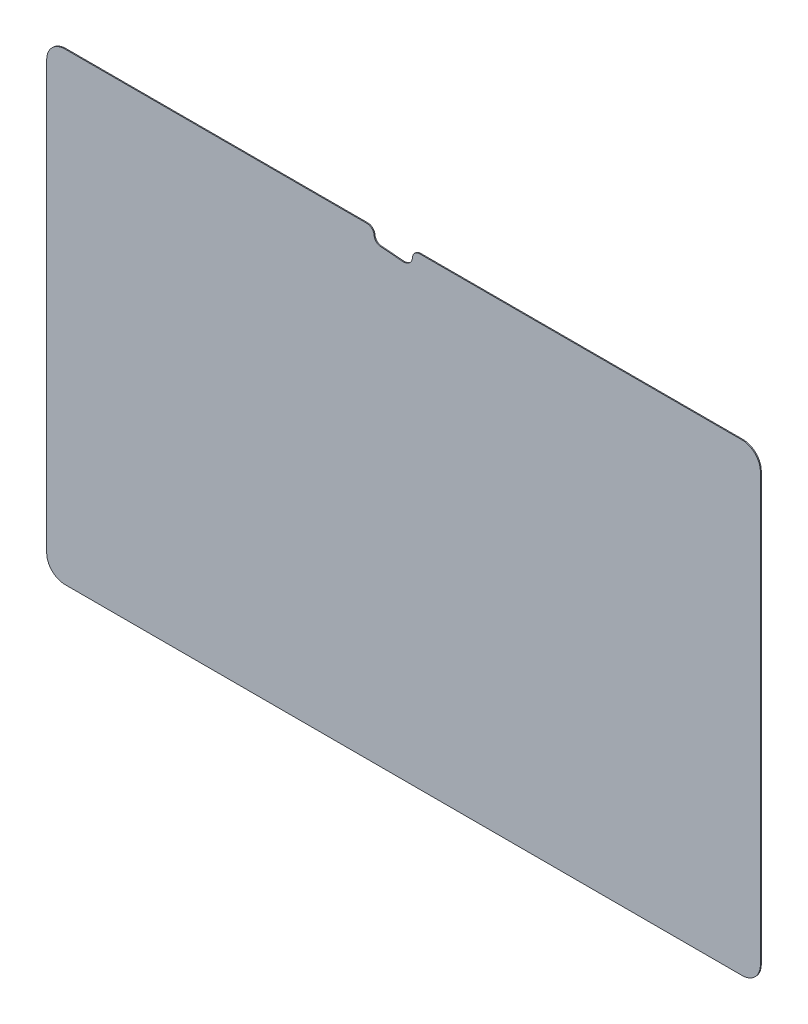
SolidWorks part; units mm, degrees
ref_plane "Front Plane" through (0, 0, 0) normal (0, 0, 1) x (1, 0, 0)
ref_plane "Top Plane" through (0, 0, 0) normal (0, 1, 0) x (1, 0, 0)
ref_plane "Right Plane" through (0, 0, 0) normal (1, 0, 0) x (0, 0, -1)
sketch "Sketch1" plane through (0, 0, 0) normal (0, 0, 1) x (1, 0, 0)
  line L1 (126.0094, -81.8896) -> (-126.0094, -81.8896)
  line L2 (126.0094, -81.8896) -> (126.0094, 81.8896)
  line L3 (126.0094, 81.8896) -> (-126.0094, 81.8896)
  line L4 (-126.0094, -81.8896) -> (-126.0094, 81.8896)
  line L5 (126.0094, -81.8896) -> (-126.0094, 81.8896) construction
  line L6 (126.0094, 81.8896) -> (-126.0094, -81.8896) construction
  point P0 (0, 0)
  dimension "D1" = 163.7792
  dimension "D2" = 252.0188
extrude "Boss-Extrude1" add sketch "Sketch1" along normal blind 0.3302
fillet "Fillet1" radius 6.4516 4 edges at (126.0094, 81.8896, 0.1651) (126.0094, -81.8896, 0.1651) (-126.0094, -81.8896, 0.1651) (-126.0094, 81.8896, 0.1651)
sketch "Sketch2" plane through (0, 0, 0.3302) normal (0, 0, 1) x (1, 0, 0)
  line L0 (-0.256, 76.5659) -> (-8.0788, 77.1989)
  line L1 (119.5578, 81.8896) -> (-119.5578, 81.8896) construction
  line L2 (2.328, 81.8896) -> (-9.212, 81.8896)
  arc A0 (-0.256, 76.5659) -> (2.328, 81.8896) centre (0, 79.7306) ccw
  arc A1 (-9.212, 81.8896) -> (-8.0788, 77.1989) centre (-7.874, 79.7306) ccw
  point P1 (0, 0)
  point P3 (0, 0)
  dimension "D1" = 6.35
  dimension "D2" = 5.08
  dimension "D3" = 79.7306
  dimension "D4" = 7.874
  dimension "D5" = 7.874
extrude "Cut-Extrude1" cut sketch "Sketch2" against normal up to next
fillet "Fillet2" radius 2.54 2 edges at (2.328, 81.8896, 0.1651) (-9.212, 81.8896, 0.1651)
